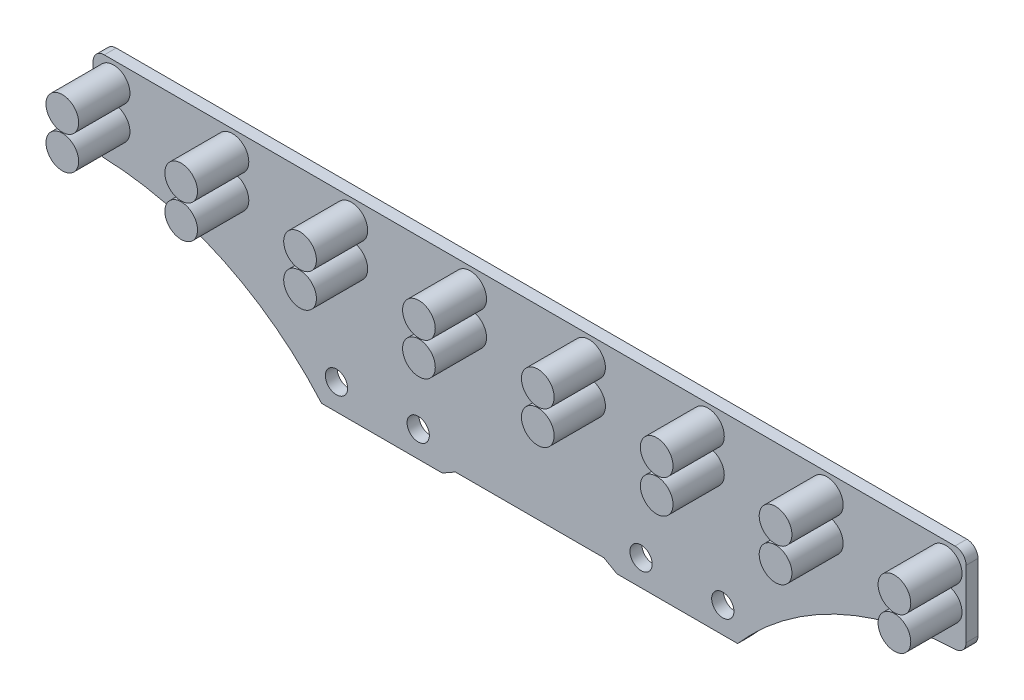
SolidWorks part; units mm, degrees
ref_plane "前视基准面" through (0, 0, 0) normal (0, 0, 1) x (1, 0, 0)
ref_plane "上视基准面" through (0, 0, 0) normal (0, 1, 0) x (1, 0, 0)
ref_plane "右视基准面" through (0, 0, 0) normal (1, 0, 0) x (0, 0, -1)
sketch "草图1" plane through (0, 0, 0) normal (0, 0, 1) x (1, 0, 0)
  line L1 (-58.75, 13) -> (58.75, 13)
  line L2 (-58.75, 13) -> (-58.75, -13)
  line L3 (-58.75, -13) -> (58.75, -13)
  line L4 (58.75, 13) -> (58.75, -13)
  line L5 (-58.75, 13) -> (58.75, -13) construction
  line L6 (-58.75, -13) -> (58.75, 13) construction
  point P0 (0, 0)
  dimension "D1" = 117.5
  dimension "D2" = 26
extrude "凸台-拉伸1" add sketch "草图1" along normal blind 1.6
sketch "草图2" plane through (0, 0, 1.6) normal (0, 0, 1) x (1, 0, 0)
  line L0 (0, 13) -> (0, 8) construction
  line L1 (58.75, 13) -> (-58.75, 13) construction
  line L2 (0, 10.25) -> (0, 5.75) construction
  line L3 (-8, 8) -> (8, 8) construction
  circle A2 centre (8, 10.25) radius 2.2
  circle A3 centre (8, 5.75) radius 2.2
  circle A4 centre (24, 10.25) radius 2.2
  circle A5 centre (24, 5.75) radius 2.2
  circle A6 centre (40, 10.25) radius 2.2
  circle A7 centre (40, 5.75) radius 2.2
  circle A8 centre (56, 10.25) radius 2.2
  circle A9 centre (56, 5.75) radius 2.2
  circle A10 centre (-8, 5.75) radius 2.2
  circle A11 centre (-8, 10.25) radius 2.2
  circle A12 centre (-24, 5.75) radius 2.2
  circle A13 centre (-24, 10.25) radius 2.2
  circle A14 centre (-40, 5.75) radius 2.2
  circle A15 centre (-40, 10.25) radius 2.2
  circle A16 centre (-56, 5.75) radius 2.2
  circle A17 centre (-56, 10.25) radius 2.2
  point P8 (0, 8)
  point P11 (0, 8)
  dimension "D3" = 16
  dimension "D4" = 4.4
  dimension "D5" = 4.4
  dimension "D1" = 5
  dimension "D2" = 4.5
  dimension "D6" = 4
  dimension "D7" = 5
extrude "凸台-拉伸4" add sketch "草图2" along normal blind 6.9
sketch "草图3" plane through (0, 0, 1.6) normal (0, 0, 1) x (1, 0, 0)
  line L0 (0, -13) -> (0, -9.5) construction
  line L1 (-58.75, -13) -> (58.75, -13) construction
  line L2 (-15, -9.5) -> (15, -9.5) construction
  line L3 (-26, -9.5) -> (26, -9.5) construction
  circle A0 centre (-15, -9.5) radius 1.5
  circle A1 centre (15, -9.5) radius 1.5
  circle A2 centre (26, -9.5) radius 1.5
  circle A3 centre (-26, -9.5) radius 1.5
  point P8 (0, -9.5)
  point P13 (0, -9.5)
  dimension "D3" = 3
  dimension "D1" = 3.5
  dimension "D2" = 30
extrude "切除-拉伸2" cut sketch "草图3" against normal blind 1.6
sketch "草图4" plane through (0, 0, 0) normal (0, 0, -1) x (-1, 0, 0)
  line L0 (0, -13) -> (0, -12) construction
  line L1 (58.75, -13) -> (-58.75, -13) construction
  line L2 (-10, -12) -> (10, -12)
  line L3 (0, -13) -> (11.75, -13)
  line L4 (0, -13) -> (-11.75, -13)
  line L5 (-11.75, -13) -> (-10, -12)
  line L6 (10, -12) -> (11.75, -13)
  point P8 (0, -12)
  point P11 (1.5563, -13)
  dimension "D1" = 1
  dimension "D2" = 20
extrude "切除-拉伸3" cut sketch "草图4" against normal blind 1.6
sketch "草图5" plane through (0, 0, 0) normal (0, 0, -1) x (-1, 0, 0)
  line L0 (0, -12) -> (0, -3) construction
  line L1 (10, -12) -> (-10, -12) construction
  line L3 (-10, -12) -> (10, -12)
  line L4 (-10, -12) -> (-10, -3)
  line L5 (-10, -3) -> (10, -3)
  line L6 (10, -12) -> (10, -3)
  line L7 (-10, -12) -> (10, -3) construction
  line L8 (-10, -3) -> (10, -12) construction
  point P5 (0, -7.5)
  dimension "D1" = 9
  dimension "D2" = 20
extrude "凸台-拉伸5" add sketch "草图5" along normal blind 9
sketch "草图6" plane through (0, 0, -9) normal (0, 0, -1) x (-1, 0, 0)
  line L0 (0, -3) -> (0, -12) construction
  line L1 (10, -3) -> (-10, -3) construction
  line L2 (-10, -12) -> (10, -12) construction
  line L4 (-9, -4) -> (9, -4)
  line L5 (-9, -4) -> (-9, -11)
  line L6 (-9, -11) -> (9, -11)
  line L7 (9, -4) -> (9, -11)
  line L8 (-9, -4) -> (9, -11) construction
  line L9 (-9, -11) -> (9, -4) construction
  point P6 (0, -7.5)
  dimension "D1" = 18
  dimension "D2" = 7
extrude "切除-拉伸4" cut sketch "草图6" against normal blind 9
fillet "圆角1" radius 1.5 2 edges at (58.75, 13, 0.8) (-58.75, 13, 0.8)
sketch "草图7" plane through (0, 0, 0) normal (0, 0, -1) x (-1, 0, 0)
  line L0 (51.4277, 13) -> (51.4277, 1) construction
  line L1 (-57.25, 13) -> (57.25, 13) construction
  line L2 (51.4277, 1) -> (58.75, 1) construction
  line L3 (58.75, 11.5) -> (58.75, -13) construction
  line L4 (26, -9.5) -> (26, -13) construction
  line L5 (58.75, -13) -> (11.75, -13) construction
  line L6 (26, -13) -> (28, -13) construction
  line L7 (28, -13) -> (58.75, -13)
  line L8 (58.75, -13) -> (58.75, 1)
  line L9 (-50.9508, 13) -> (-50.9508, 1) construction
  line L10 (-50.9508, 1) -> (-58.75, 1) construction
  line L11 (-58.75, -13) -> (-58.75, 11.5) construction
  line L12 (-26, -9.5) -> (-26, -13) construction
  line L13 (-11.75, -13) -> (-58.75, -13) construction
  line L14 (-26, -13) -> (-28, -13) construction
  line L15 (-58.75, 1) -> (-58.75, -13)
  line L16 (-58.75, -13) -> (-28, -13)
  arc A0 (58.75, 1) -> (28, -13) centre (58.75, -39.7701) ccw
  arc A1 (-58.75, 1) -> (-28, -13) centre (-58.75, -39.7701) cw
  dimension "D3" = 12
  dimension "D4" = 2
  dimension "D1" = 12
  dimension "D2" = 2
extrude "切除-拉伸5" cut sketch "草图7" against normal blind 1.6
fillet "圆角2" radius 1.5 2 edges at (-58.75, 1, 0.8) (58.75, 1, 0.8)
sketch "草图8" plane through (0, 0, 0) normal (0, 0, -1) x (-1, 0, 0)
  line L0 (0, 13) -> (0, -12) construction
  line L1 (-57.25, 13) -> (57.25, 13) construction
  line L2 (-10, -12) -> (10, -12) construction
